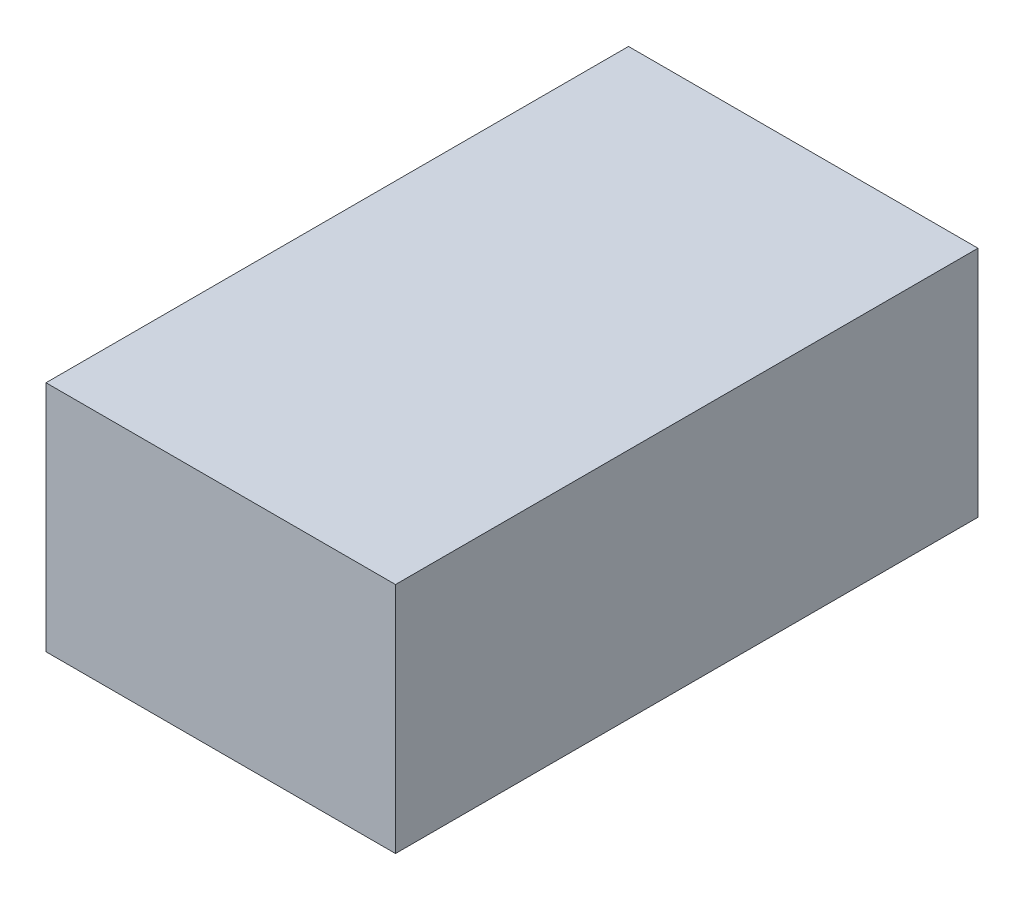
SolidWorks part; units mm, degrees
ref_plane "Front Plane" through (0, 0, 0) normal (0, 0, 1) x (1, 0, 0)
ref_plane "Top Plane" through (0, 0, 0) normal (0, 1, 0) x (1, 0, 0)
ref_plane "Right Plane" through (0, 0, 0) normal (1, 0, 0) x (0, 0, -1)
sketch "Sketch2" plane through (0, 0, 0) normal (1, 0, 0) x (0, 0, -1)
  line L1 (-50, -20) -> (50, -20)
  line L2 (-50, -20) -> (-50, 20)
  line L3 (-50, 20) -> (50, 20)
  line L4 (50, -20) -> (50, 20)
  line L5 (-50, -20) -> (50, 20) construction
  line L6 (-50, 20) -> (50, -20) construction
  point P0 (0, 0)
  dimension "D1" = 100
  dimension "D2" = 40
extrude "Boss-Extrude1" add sketch "Sketch2" along normal blind 60
